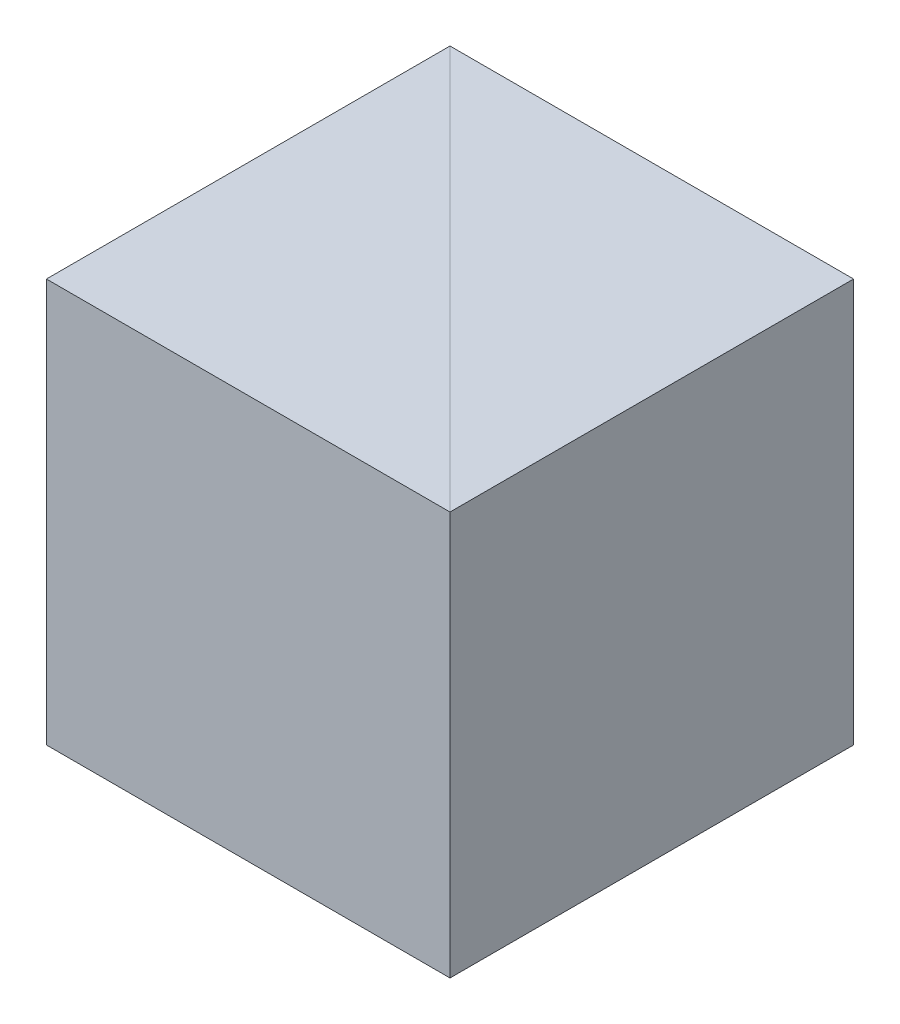
SolidWorks part; units mm, degrees
ref_plane "前视基准面" through (0, 0, 0) normal (0, 0, 1) x (1, 0, 0)
ref_plane "上视基准面" through (0, 0, 0) normal (0, 1, 0) x (1, 0, 0)
ref_plane "右视基准面" through (0, 0, 0) normal (1, 0, 0) x (0, 0, -1)
sketch "草图1" plane through (0, 0, 0) normal (0, 1, 0) x (1, 0, 0)
  line L0 (0, 0) -> (0, 10)
  line L1 (0, 10) -> (-10, 10)
  line L2 (-10, 10) -> (0, 0)
  dimension "D1" = 10
  dimension "D2" = 10
extrude "凸台-拉伸1" add sketch "草图1" along normal blind 10
sketch "草图2" plane through (0, 0, 0) normal (0, -1, 0) x (1, 0, 0)
  line L0 (-10, -10) -> (-10, 0)
  line L1 (-10, 0) -> (0, 0)
  line L2 (0, 0) -> (-10, -10)
extrude "凸台-拉伸2" add sketch "草图2" against normal blind 10 separate body
